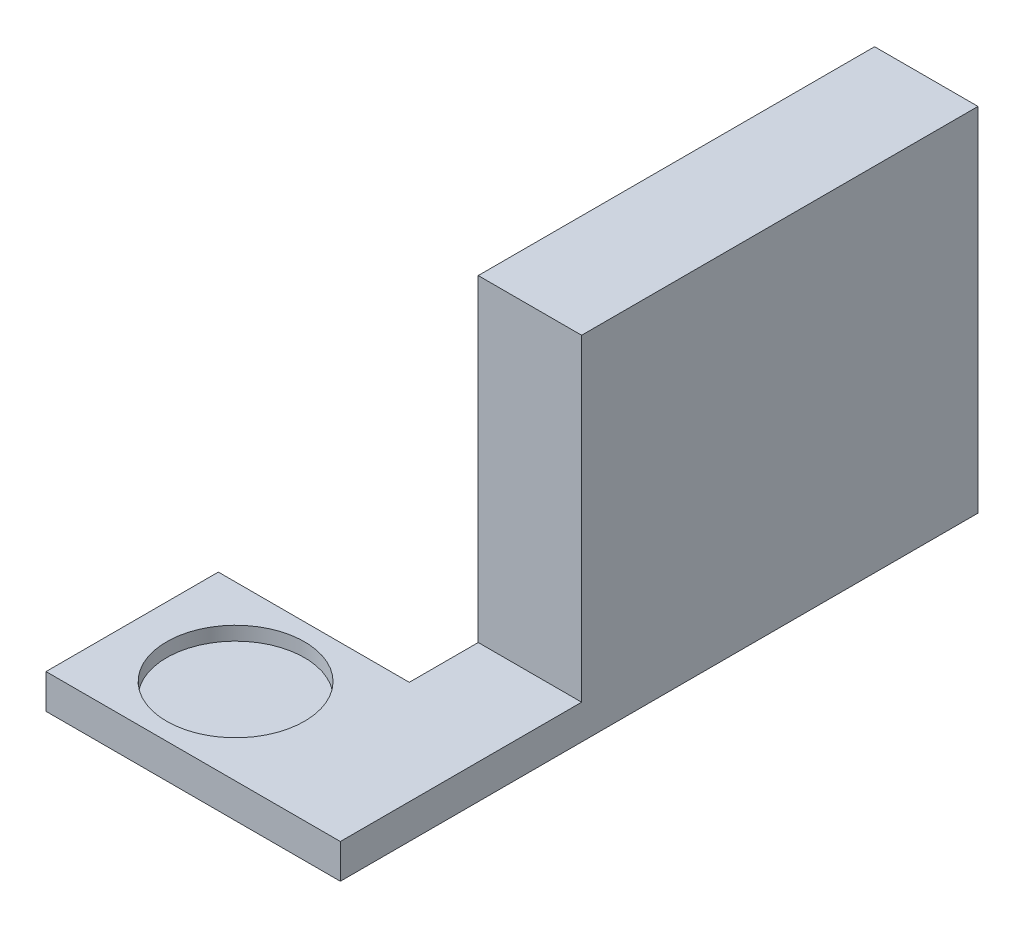
SolidWorks part; units mm, degrees
ref_plane "Front Plane" through (0, 0, 0) normal (0, 0, 1) x (1, 0, 0)
ref_plane "Top Plane" through (0, 0, 0) normal (0, 1, 0) x (1, 0, 0)
ref_plane "Right Plane" through (0, 0, 0) normal (1, 0, 0) x (0, 0, -1)
sketch "Sketch1" plane through (0, 0, 0) normal (0, 1, 0) x (1, 0, 0)
  line L1 (-50, -20) -> (50, -20)
  line L2 (-50, -20) -> (-50, 20)
  line L3 (-50, 20) -> (50, 20)
  line L4 (50, -20) -> (50, 20)
  line L5 (-50, -20) -> (50, 20) construction
  line L6 (-50, 20) -> (50, -20) construction
  point P0 (0, 0)
  dimension "D1" = 100
  dimension "D2" = 40
extrude "Boss-Extrude1" add sketch "Sketch1" along normal blind 15
other "Move Face4" face at (50, 7.5, 0) parameters "D1"=5
sketch "Sketch5" plane through (0, 15, 0) normal (0, 1, 0) x (1, 0, 0)
  circle A0 centre (40, 0) radius 10
extrude "Cut-Extrude2" cut sketch "Sketch5" against normal blind 2
other "Move Face5" face at (2.5, 7.5, -20) face at (2.5, 7.5, 20) parameters "D1"=7.5
other "Move Face7" face at (-50, 7.5, 0) parameters "D1"=75
other "Move Face8" face at (40, 0, 0) parameters "D1"=5
other "Move Face9" face at (55, 10, 0) parameters "D1"=12.7
sketch "Sketch6" plane through (0, 0, -12.5) normal (0, 0, -1) x (-1, 0, 0)
  line L0 (-67.7, 15) -> (-25, 15) construction
  line L1 (-67.7, 5) -> (-52.7, 5)
  line L2 (-67.7, 5) -> (-67.7, 15)
  line L3 (-67.7, 15) -> (-52.7, 15)
  line L4 (-52.7, 5) -> (-52.7, 15)
  dimension "D1" = 15
extrude "Boss-Extrude2" add sketch "Sketch6" along normal blind 100
other "Move Face10" face at (60.2, 10, -112.5) parameters "D1"=22.5
sketch "Sketch7" plane through (0, 15, 0) normal (0, 1, 0) x (1, 0, 0)
  line L1 (67.7, 90) -> (52.7, 90)
  line L2 (67.7, 90) -> (67.7, 12.5)
  line L3 (67.7, 12.5) -> (52.7, 12.5)
  line L4 (52.7, 90) -> (52.7, 12.5)
extrude "Boss-Extrude3" add sketch "Sketch7" along normal blind 47.8
other "Move Face11" face at (48.4667, 5, -30) parameters "D1"=5
other "Move Face12" face at (60.2, 62.8, -51.25) parameters "D1"=6.7
other "Move Face13" face at (60.2, 56.1, -51.25) parameters "D1"=4.1
other "Move Face16" face at (60.2, 60.2, -51.25) parameters "D1"=0.9
other "Move Face17" face at (60.2, 38.05, -12.5) parameters "D1"=10
other "Move Face18" face at (60.2, 35.55, -90) parameters "D1"=10
